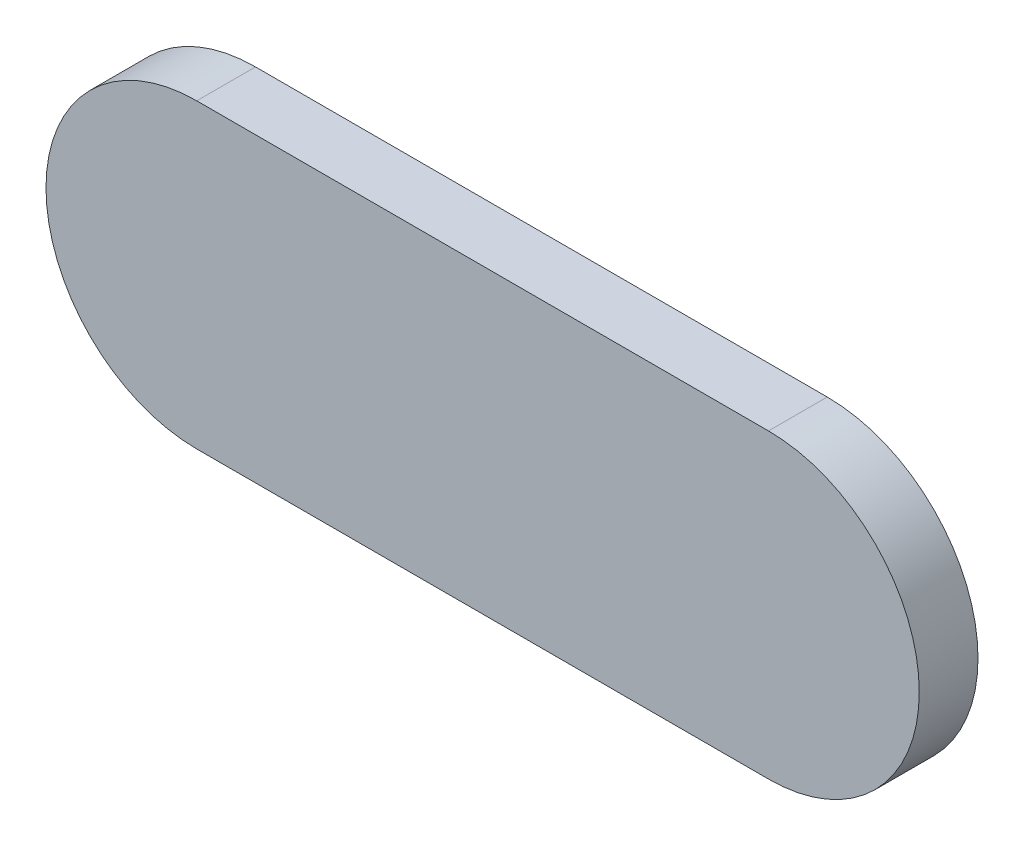
SolidWorks part; units mm, degrees
ref_plane "前视基准面" through (0, 0, 0) normal (0, 0, 1) x (1, 0, 0)
ref_plane "上视基准面" through (0, 0, 0) normal (0, 1, 0) x (1, 0, 0)
ref_plane "右视基准面" through (0, 0, 0) normal (1, 0, 0) x (0, 0, -1)
sketch "草图1" plane through (0, 0, 0) normal (0, 0, 1) x (1, 0, 0)
  line L3 (7.3, 3.85) -> (-7.3, 3.85)
  line L5 (-7.3, -3.85) -> (7.3, -3.85)
  arc A0 (7.3, -3.85) -> (7.3, 3.85) centre (7.3, 0) ccw
  arc A1 (-7.3, 3.85) -> (-7.3, -3.85) centre (-7.3, 0) ccw
extrude "凸台-拉伸1" add sketch "草图1" along normal blind 1.5
sketch "草图2" plane through (0, 0, 0) normal (0, 0, -1) x (-1, 0, 0)
  line L0 (-7.35, 2.3) -> (7.35, 2.3)
  line L1 (-7.35, -2.3) -> (7.35, -2.3)
  arc A0 (7.35, -2.3) -> (7.35, 2.3) centre (7.35, 0) ccw
  arc A1 (-7.35, -2.3) -> (-7.35, 2.3) centre (-7.35, 0) cw
extrude "凸台-拉伸2" add sketch "草图2" along normal blind 0.5
sketch "草图3" plane through (0, 0, -0.5) normal (0, 0, -1) x (-1, 0, 0)
  circle A0 centre (1.27, 0) radius 0.75
  circle A1 centre (3.81, 0) radius 0.75
  circle A2 centre (-3.81, 0) radius 0.75
  circle A3 centre (-1.27, 0) radius 0.75
extrude "凸台-拉伸3" add sketch "草图3" along normal blind 1
fillet "圆角2" radius 0.5 4 edges at (4.56, 0, -1.5) (-4.56, 0, -1.5) (-2.02, 0, -1.5) (2.02, 0, -1.5)
